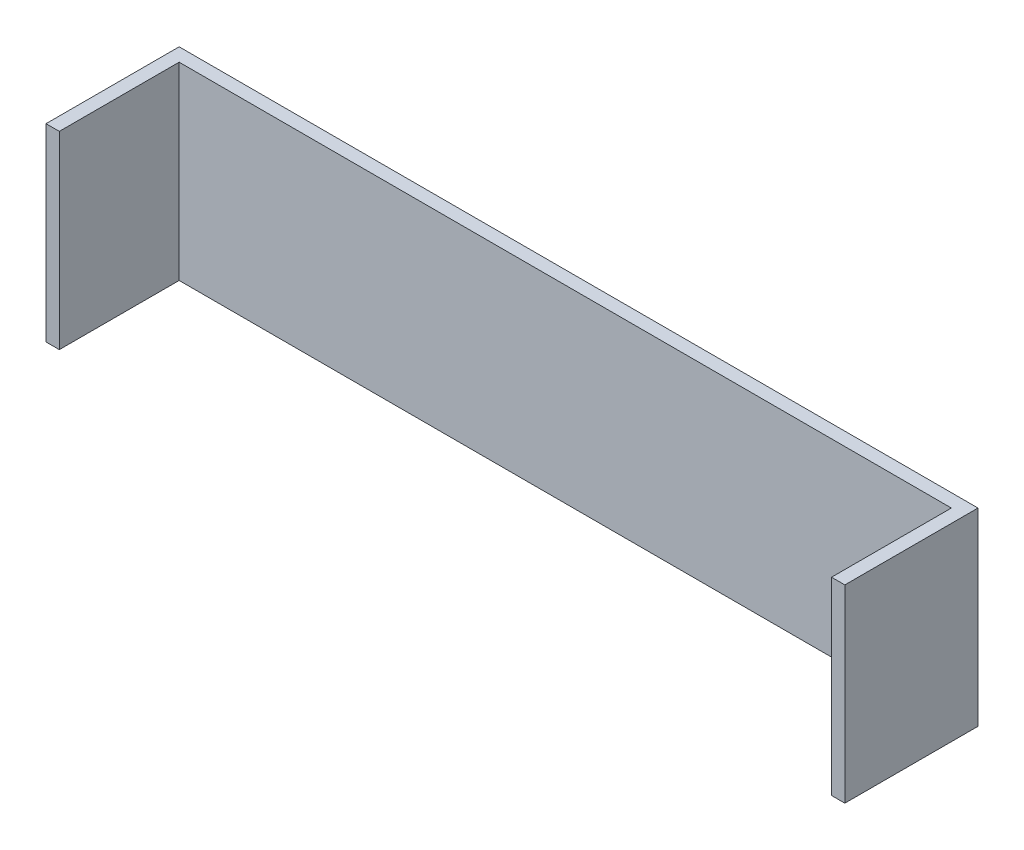
SolidWorks part; units mm, degrees
ref_plane "Front Plane" through (0, 0, 0) normal (0, 0, 1) x (1, 0, 0)
ref_plane "Top Plane" through (0, 0, 0) normal (0, 1, 0) x (1, 0, 0)
ref_plane "Right Plane" through (0, 0, 0) normal (1, 0, 0) x (0, 0, -1)
sketch "Sketch1" plane through (0, 0, 0) normal (0, 1, 0) x (1, 0, 0)
  line L0 (-190.5, 0) -> (190.5, 0)
  line L1 (-190.5, 0) -> (-190.5, -63.5)
  line L2 (190.5, 0) -> (190.5, -63.5)
  point P3 (0, 0)
  dimension "D1" = 381
  dimension "D2" = 63.5
extrude "Extrude-Thin1" add sketch "Sketch1" along normal mid plane 90.17 thin
